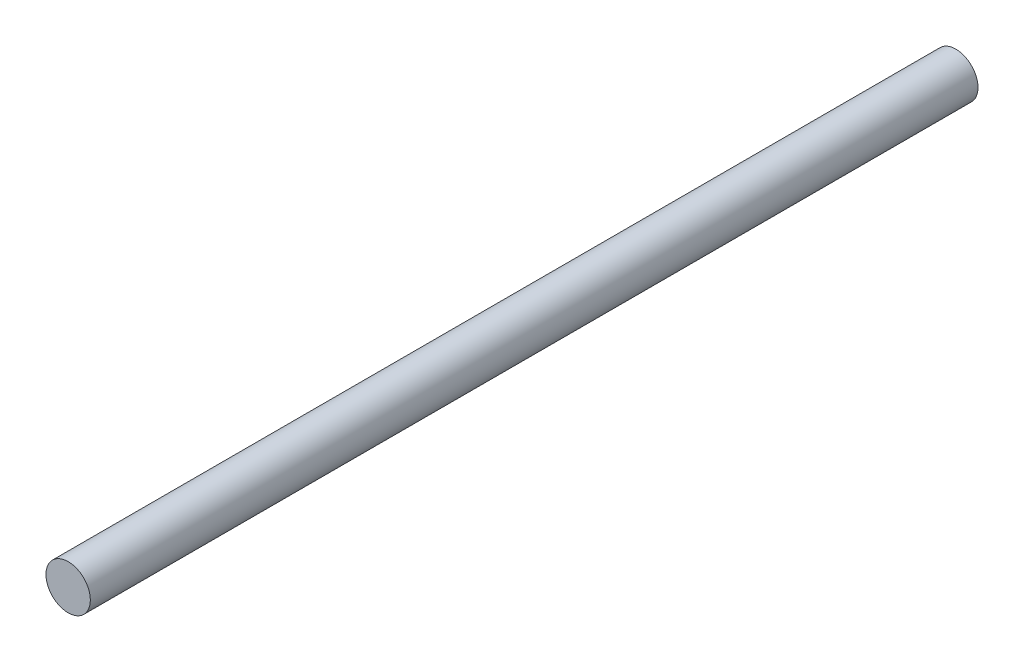
SolidWorks part; units mm, degrees
ref_plane "Piano frontale" through (0, 0, 0) normal (0, 0, 1) x (1, 0, 0)
ref_plane "Piano superiore" through (0, 0, 0) normal (0, 1, 0) x (1, 0, 0)
ref_plane "Piano destro" through (0, 0, 0) normal (1, 0, 0) x (0, 0, -1)
sketch "Schizzo1" plane through (0, 0, 0) normal (0, 0, 1) x (1, 0, 0)
  circle A0 centre (0, 0) radius 2.5
  dimension "D1" = 5
extrude "Estrusione-Estrusione1" add sketch "Schizzo1" along normal blind 100
sketch "Schizzo2" plane through (0, 0, 0) normal (0, 1, 0) x (1, 0, 0)
  line L0 (2.5, 0) -> (-2.5, 0) construction
  circle A0 centre (0, -1) radius 0.5
  dimension "D1" = 1
  dimension "D2" = 1
extrude "Taglio-Estrusione1" cut sketch "Schizzo2" against normal through all
sketch "Schizzo3" plane through (0, 0, 0) normal (0, 1, 0) x (1, 0, 0)
  line L0 (-2.5, -100) -> (2.5, -100) construction
  circle A0 centre (0, -99) radius 0.5
  dimension "D1" = 1
  dimension "D2" = 1
extrude "Taglio-Estrusione2" cut sketch "Schizzo3" against normal through all
